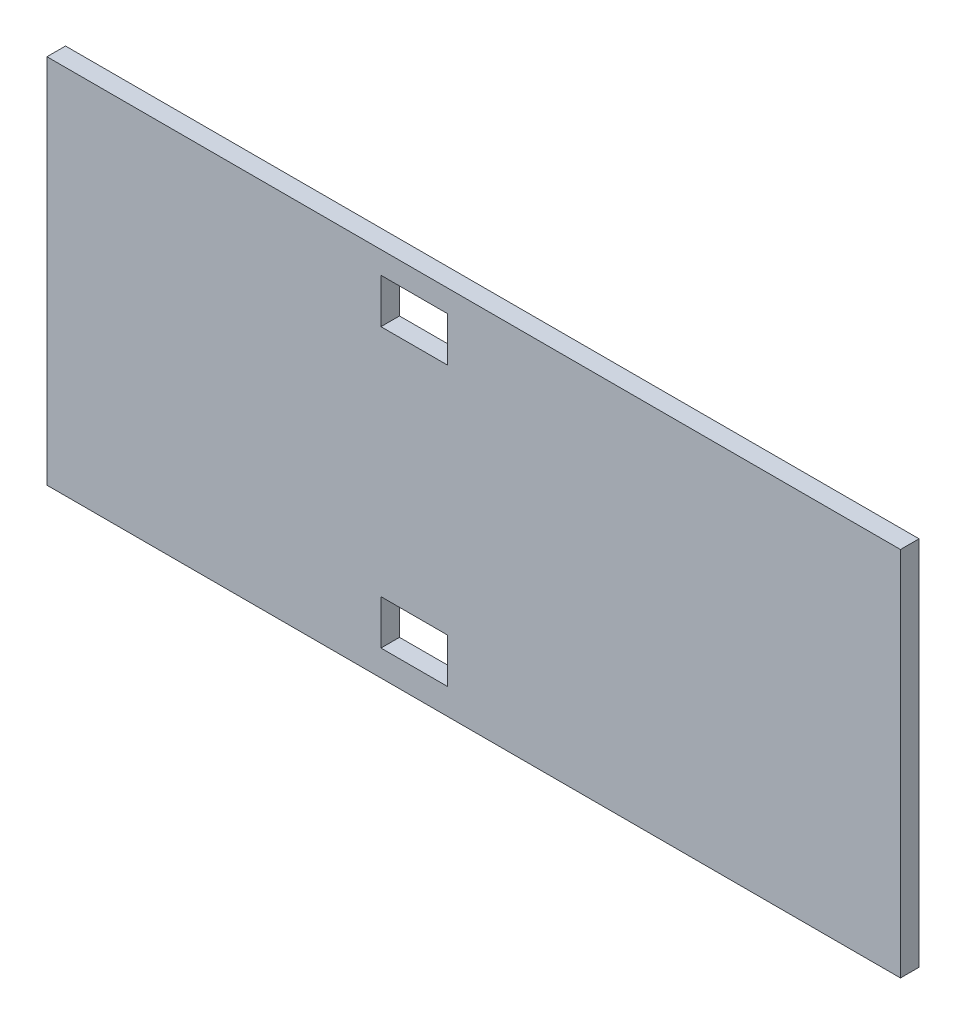
SolidWorks part; units mm, degrees
ref_plane "Front Plane" through (0, 0, 0) normal (0, 0, 1) x (1, 0, 0)
ref_plane "Top Plane" through (0, 0, 0) normal (0, 1, 0) x (1, 0, 0)
ref_plane "Right Plane" through (0, 0, 0) normal (1, 0, 0) x (0, 0, -1)
sketch "Sketch1" plane through (0, 0, 0) normal (0, 0, 1) x (1, 0, 0)
  line L1 (0, 0) -> (292.1, 0)
  line L2 (0, 0) -> (0, 127)
  line L3 (0, 127) -> (292.1, 127)
  line L4 (292.1, 0) -> (292.1, 127)
  dimension "D1" = 292.1
  dimension "D2" = 127
extrude "Boss-Extrude1" add sketch "Sketch1" along normal blind 6.35 contours L3 L4 L1 L2
sketch "Sketch2" plane through (0, 0, 6.35) normal (0, 0, 1) x (1, 0, 0)
  line L1 (114.3, 24.13) -> (137.16, 24.13)
  line L2 (114.3, 24.13) -> (114.3, 8.89)
  line L3 (114.3, 8.89) -> (137.16, 8.89)
  line L4 (137.16, 24.13) -> (137.16, 8.89)
  line L7 (0, 0) -> (0, 127) construction
  line L8 (0, 0) -> (292.1, 0) construction
  dimension "D1" = 8.89
  dimension "D2" = 114.3
  dimension "D3" = 15.24
  dimension "D4" = 22.86
extrude "Cut-Extrude1" cut sketch "Sketch2" against normal blind 6.35
pattern_linear "LPattern1" count 2 spacing 95.25 along (0, 1, 0) of "Cut-Extrude1"
